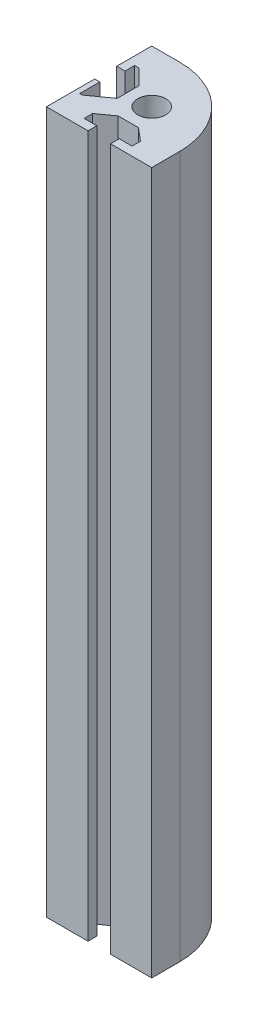
SolidWorks part; units mm, degrees
ref_plane "Front" through (0, 0, 0) normal (0, 0, 1) x (1, 0, 0)
ref_plane "Top" through (0, 0, 0) normal (0, 1, 0) x (1, 0, 0)
ref_plane "Right" through (0, 0, 0) normal (1, 0, 0) x (0, 0, -1)
sketch "Croquis1" plane through (0, 0, 0) normal (0, 1, 0) x (1, 0, 0)
  line L0 (-7, 15) -> (-15, 15)
  line L1 (-15, 15) -> (15, 15) construction
  line L2 (-15, 15) -> (-15, -15) construction
  line L3 (-15, -15) -> (15, -15) construction
  line L4 (15, 15) -> (15, -15) construction
  line L5 (-15, 15) -> (15, -15) construction
  line L6 (-15, -15) -> (15, 15) construction
  line L7 (-15, 15) -> (-15, 5.0276)
  line L8 (-15, 5.0276) -> (-12.6234, 5.0276)
  line L9 (-12.6234, 5.0276) -> (-12.6234, 7.7527)
  line L10 (-12.6234, 7.7527) -> (-11.3205, 7.7527)
  line L11 (-11.3205, 7.7527) -> (-7, 3.4321)
  line L12 (-7, 3.4321) -> (-7, -2.8611)
  line L13 (-7, -2.8611) -> (-12.793, -7)
  line L14 (-12.793, -7) -> (-13.5273, -7)
  line L15 (-13.5273, -7) -> (-13.5273, -1.258)
  line L16 (-13.5273, -1.258) -> (-15, -1.258)
  line L17 (-15, -1.258) -> (-15, -15)
  line L18 (-15, -15) -> (-3.1399, -15)
  line L19 (-3.1399, -15) -> (-3.1399, -12.5058)
  line L20 (-3.1399, -12.5058) -> (-6.779, -12.5058)
  line L21 (-6.779, -12.5058) -> (-6.779, -10.0798)
  line L22 (-6.779, -10.0798) -> (-2.5129, -7.0319)
  line L23 (-2.5129, -7.0319) -> (3.2559, -7.0319)
  line L24 (3.2559, -7.0319) -> (6.8949, -10.0798)
  line L25 (6.8949, -10.0798) -> (6.8949, -12.5058)
  line L26 (6.8949, -12.5058) -> (3.2559, -12.5058)
  line L27 (3.2559, -12.5058) -> (3.2559, -15)
  line L28 (3.2559, -15) -> (15, -15)
  line L29 (15, -15) -> (15, -7)
  line L30 (0, 0) -> (-50000, 0) construction
  line L31 (0, 0) -> (0, -50000) construction
  circle A0 centre (0, 0) radius 4
  arc A1 (-7, 15) -> (15, -7) centre (-7, -7) cw
  point P0 (0, 0)
  point P24 (-11.3205, 7.7527)
  dimension "D3" = 8
  dimension "D4" = 22
  dimension "D1" = 30
  dimension "D2" = 30
extrude "Saliente-Extruir1" add sketch "Croquis1" along normal blind 200
